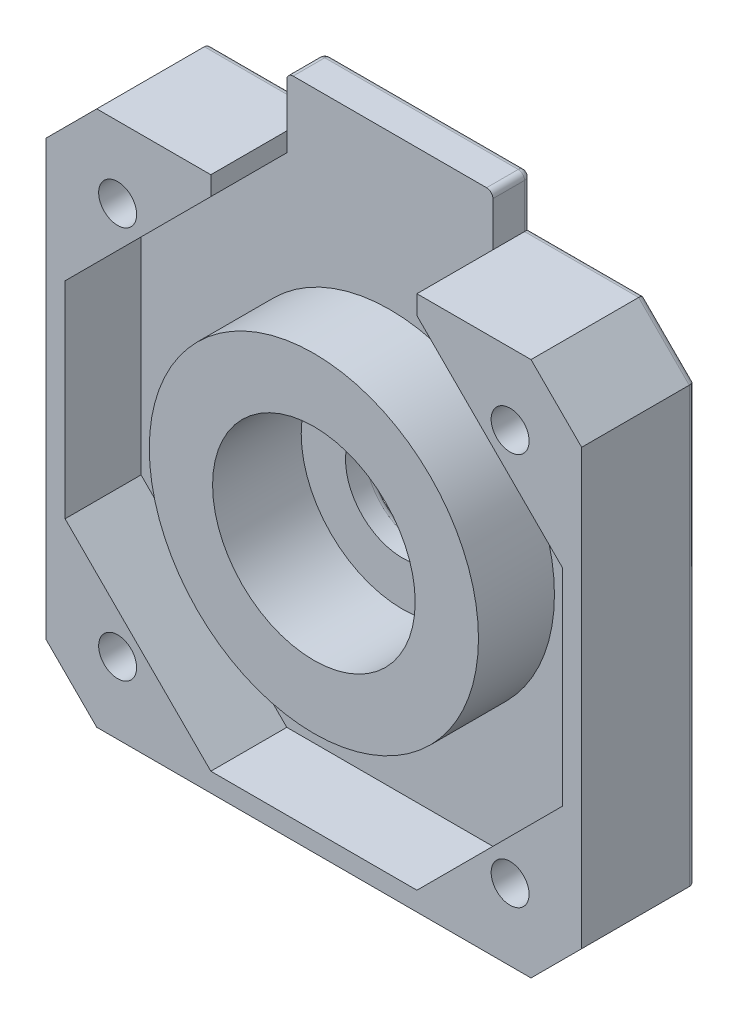
SolidWorks part; units mm, degrees
ref_plane "Front Plane" through (0, 0, 0) normal (0, 0, 1) x (1, 0, 0)
ref_plane "Top Plane" through (0, 0, 0) normal (0, 1, 0) x (1, 0, 0)
ref_plane "Right Plane" through (0, 0, 0) normal (1, 0, 0) x (0, 0, -1)
sketch "Sketch2" plane through (0, 0, 0) normal (0, 0, 1) x (1, 0, 0)
  line L0 (-21.15, 17.15) -> (-17.15, 21.15)
  line L1 (-17.15, -21.15) -> (17.15, -21.15)
  line L2 (-21.15, -17.15) -> (-21.15, 17.15)
  line L3 (-17.15, 21.15) -> (17.15, 21.15)
  line L4 (21.15, -17.15) -> (21.15, 17.15)
  line L5 (-21.15, -21.15) -> (21.15, 21.15) construction
  line L6 (-21.15, 21.15) -> (21.15, -21.15) construction
  line L7 (17.15, 21.15) -> (21.15, 17.15)
  line L8 (17.15, -21.15) -> (21.15, -17.15)
  line L9 (-21.15, -17.15) -> (-17.15, -21.15)
  point P0 (0, 0)
  dimension "D1" = 42.3
  dimension "D2" = 42.3
extrude "Boss-Extrude1" add sketch "Sketch2" along normal blind 9
sketch "Sketch9" plane through (0, 0, 9) normal (0, 0, 1) x (1, 0, 0)
  line L2 (-8.1393, 19.65) -> (-19.65, 8.1393)
  line L3 (-19.65, 8.1393) -> (-19.65, -8.1393)
  line L4 (-19.65, -8.1393) -> (-8.1393, -19.65)
  line L5 (-8.1393, -19.65) -> (8.1393, -19.65)
  line L6 (8.1393, -19.65) -> (19.65, -8.1393)
  line L7 (19.65, -8.1393) -> (19.65, 8.1393)
  line L8 (19.65, 8.1393) -> (8.1393, 19.65)
  line L9 (21.15, -17.15) -> (21.15, 17.15) construction
  line L10 (-21.15, 17.15) -> (-21.15, -17.15) construction
  line L11 (8.1393, 19.65) -> (-8.1393, 19.65) [skipped]
  line L12 (-8.1393, 19.65) -> (-8.1393, 21.15)
  line L13 (17.15, 21.15) -> (-17.15, 21.15) construction
  line L14 (-8.1393, 21.15) -> (8.1393, 21.15)
  line L15 (8.1393, 21.15) -> (8.1393, 19.65)
  circle A0 centre (0, 0) radius 19.65 construction
  circle A1 centre (0, 0) radius 13
  dimension "D2" = 26
  dimension "D1" = 1.5
extrude "Cut-Extrude6" cut sketch "Sketch9" against normal blind 6
sketch "Sketch10" plane through (0, 0, 9) normal (0, 0, 1) x (1, 0, 0)
  circle A0 centre (0, 0) radius 8
  dimension "D1" = 16
extrude "Cut-Extrude7" cut sketch "Sketch10" against normal blind 7
sketch "Sketch11" plane through (0, 0, 2) normal (0, 0, 1) x (1, 0, 0)
  circle A0 centre (0, 0) radius 4.5
  dimension "D1" = 9
extrude "Cut-Extrude8" cut sketch "Sketch11" against normal through all
sketch "Sketch13" plane through (0, 0, 9) normal (0, 0, 1) x (1, 0, 0)
  line L1 (15.5, -15.5) -> (-15.5, -15.5) construction
  line L2 (15.5, -15.5) -> (15.5, 15.5) construction
  line L3 (15.5, 15.5) -> (-15.5, 15.5) construction
  line L4 (-15.5, -15.5) -> (-15.5, 15.5) construction
  line L5 (15.5, -15.5) -> (-15.5, 15.5) construction
  line L6 (15.5, 15.5) -> (-15.5, -15.5) construction
  circle A0 centre (-15.5, -15.5) radius 1.5
  circle A1 centre (-15.5, 15.5) radius 1.5
  circle A2 centre (15.5, 15.5) radius 1.5
  circle A3 centre (15.5, -15.5) radius 1.5
  point P0 (0, 0)
  dimension "D3" = 3
  dimension "D1" = 31
  dimension "D2" = 31
extrude "Cut-Extrude9" cut sketch "Sketch13" against normal through all
sketch "Sketch14" plane through (0, 0, 0) normal (0, 0, -1) x (-1, 0, 0)
  line L1 (-15.5, 15.5) -> (15.5, 15.5) construction
  line L2 (-15.5, 15.5) -> (-15.5, -15.5) construction
  line L3 (-15.5, -15.5) -> (15.5, -15.5) construction
  line L4 (15.5, 15.5) -> (15.5, -15.5) construction
  circle A0 centre (-15.5, 15.5) radius 3.1
  circle A1 centre (15.5, 15.5) radius 3.1
  circle A2 centre (-15.5, -15.5) radius 3.1
  circle A3 centre (15.5, -15.5) radius 3.1
  dimension "D1" = 6.2
sketch "Sketch15" plane through (0, 21.15, 0) normal (0, 1, 0) x (1, 0, 0)
  line L0 (17.15, 0) -> (-17.15, 0) construction
  line L1 (-8.1393, -3) -> (8.1393, -3)
  line L2 (-8.1393, -3) -> (-8.1393, 0)
  line L3 (-8.1393, 0) -> (8.1393, 0)
  line L4 (8.1393, -3) -> (8.1393, 0)
extrude "Cut-Extrude11" cut sketch "Sketch14" against normal blind 2.5
extrude "Boss-Extrude3" add sketch "Sketch15" along normal blind 4
fillet "Fillet4" radius 0.5 19 edges at (-19.15, -19.15, 0) (0, -21.15, 0) (19.15, -19.15, 0) (21.15, 0, 0) (19.15, 19.15, 0) (12.6446, 21.15, 0) (8.1393, 23.15, 0) (0, 25.15, 0) (-8.1393, 23.15, 0) (-12.6446, 21.15, 0) (-19.15, 19.15, 0) (-21.15, 0, 0) (4.5, 0, 0) (12.4, 15.5, 0) (-18.6, -15.5, 0) (12.4, -15.5, 0) (-18.6, 15.5, 0) (8.1393, 25.15, 1.5) (-8.1393, 25.15, 1.5)
